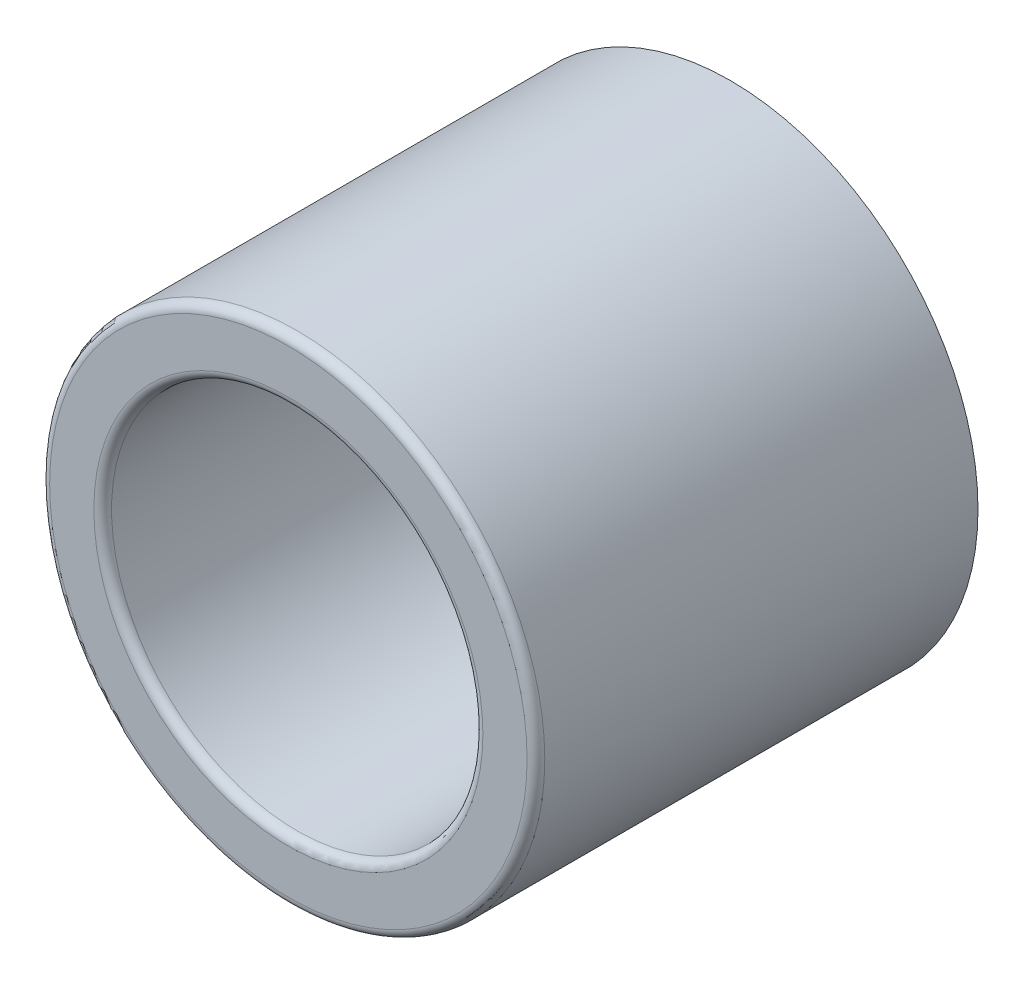
SolidWorks part; units mm, degrees
ref_plane "Front Plane" through (0, 0, 0) normal (0, 0, 1) x (1, 0, 0)
ref_plane "Top Plane" through (0, 0, 0) normal (0, 1, 0) x (1, 0, 0)
ref_plane "Right Plane" through (0, 0, 0) normal (1, 0, 0) x (0, 0, -1)
sketch "Sketch1" plane through (0, 0, 0) normal (0, 0, 1) x (1, 0, 0)
  circle A0 centre (0, 0) radius 2.8
  circle A1 centre (0, 0) radius 2.1
  dimension "D1" = 5.6
  dimension "D2" = 4.2
extrude "Boss-Extrude1" add sketch "Sketch1" along normal blind 5
fillet "Fillet1" radius 0.1 2 edges at (2.1, 0, 5) (2.8, 0, 5)
